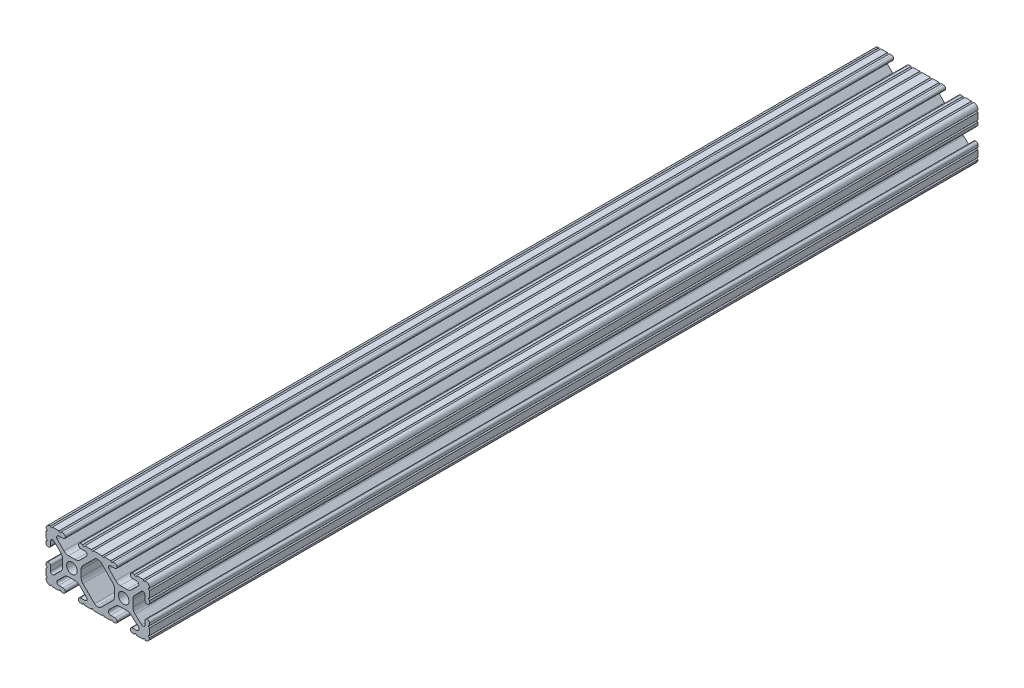
SolidWorks part; units mm, degrees
ref_plane "Front Plane" through (0, 0, 0) normal (0, 0, 1) x (1, 0, 0)
ref_plane "Top Plane" through (0, 0, 0) normal (0, 1, 0) x (1, 0, 0)
ref_plane "Right Plane" through (0, 0, 0) normal (1, 0, 0) x (0, 0, -1)
sketch "Sketch1" plane through (0, 0, 0) normal (0, 0, 1) x (1, 0, 0)
  line L0 (-7.2595, -3.8694) -> (-1.5457, -9.5728)
  line L1 (-8.1915, 1.6223) -> (-8.1915, -1.6223)
  line L2 (-1.504, 9.5765) -> (-7.252, 3.8768)
  line L3 (0.5515, 10.033) -> (-0.3952, 10.033)
  line L4 (7.2829, 3.8459) -> (1.6756, 9.5611)
  line L5 (8.1915, -1.6223) -> (8.1915, 1.6223)
  line L6 (1.5457, -9.5728) -> (7.2595, -3.8694)
  line L7 (-0.4332, -10.033) -> (0.4332, -10.033)
  line L8 (18.0171, 12.7) -> (16.9875, 12.7)
  line L9 (15.9385, 11.651) -> (15.9385, 11.5392)
  line L10 (16.9875, 10.4902) -> (19.1164, 10.4902)
  line L11 (19.8441, 8.7652) -> (16.619, 5.4551)
  line L12 (14.3449, 4.4958) -> (11.0833, 4.4958)
  line L13 (8.817, 5.4472) -> (5.5642, 8.7627)
  line L14 (6.2894, 10.4902) -> (8.4125, 10.4902)
  line L15 (9.4615, 11.5392) -> (9.4615, 11.651)
  line L16 (8.4125, 12.7) -> (7.3829, 12.7)
  line L17 (6.3669, 12.7) -> (3.1496, 12.7)
  line L18 (2.1336, 12.7) -> (-2.1336, 12.7)
  line L19 (-3.1496, 12.7) -> (-6.3669, 12.7)
  line L20 (-7.3829, 12.7) -> (-8.4125, 12.7)
  line L21 (-9.4615, 11.651) -> (-9.4615, 11.5392)
  line L22 (-8.4125, 10.4902) -> (-6.2836, 10.4902)
  line L23 (-5.5326, 8.6661) -> (-8.81, 5.4163)
  line L24 (-11.0455, 4.4958) -> (-14.3545, 4.4958)
  line L25 (-16.59, 5.4163) -> (-19.8674, 8.6661)
  line L26 (-19.1164, 10.4902) -> (-16.9875, 10.4902)
  line L27 (-15.9385, 11.5392) -> (-15.9385, 11.651)
  line L28 (-16.9875, 12.7) -> (-18.0171, 12.7)
  line L29 (-19.0331, 12.7) -> (-22.2504, 12.7)
  line L30 (-25.4, 9.5504) -> (-25.4, 6.3331)
  line L31 (-25.4, 5.3171) -> (-25.4, 4.2375)
  line L32 (-24.401, 3.2385) -> (-24.2392, 3.2385)
  line L33 (-23.1902, 4.2875) -> (-23.1902, 6.3347)
  line L34 (-21.434, 7.0665) -> (-18.148, 3.8082)
  line L35 (-17.2085, 1.5536) -> (-17.2085, -1.6952)
  line L36 (-18.1405, -3.9423) -> (-21.4316, -7.2274)
  line L37 (-23.1902, -6.498) -> (-23.1902, -4.2875)
  line L38 (-24.2392, -3.2385) -> (-24.351, -3.2385)
  line L39 (-25.4, -4.2875) -> (-25.4, -5.3171)
  line L40 (-25.4, -6.3331) -> (-25.4, -9.5504)
  line L41 (-22.2504, -12.7) -> (-19.0331, -12.7)
  line L42 (-18.0171, -12.7) -> (-16.9875, -12.7)
  line L43 (-15.9384, -11.651) -> (-15.9384, -11.5392)
  line L44 (-16.9875, -10.4902) -> (-19.1164, -10.4902)
  line L45 (-19.8341, -8.7551) -> (-16.4966, -5.4237)
  line L46 (-14.2536, -4.4958) -> (-11.1464, -4.4958)
  line L47 (-8.9034, -5.4237) -> (-5.5659, -8.7551)
  line L48 (-6.2836, -10.4902) -> (-8.4125, -10.4902)
  line L49 (-9.4616, -11.5392) -> (-9.4616, -11.651)
  line L50 (-8.4125, -12.7) -> (-7.3829, -12.7)
  line L51 (-6.3669, -12.7) -> (-3.1496, -12.7)
  line L52 (-2.1336, -12.7) -> (2.1336, -12.7)
  line L53 (3.1496, -12.7) -> (6.3669, -12.7)
  line L54 (7.3829, -12.7) -> (8.4125, -12.7)
  line L55 (9.4616, -11.651) -> (9.4616, -11.5392)
  line L56 (8.4125, -10.4902) -> (6.2894, -10.4902)
  line L57 (5.4807, -8.5353) -> (8.5979, -5.4237)
  line L58 (10.8409, -4.4958) -> (14.1026, -4.4958)
  line L59 (16.1879, -5.2766) -> (19.8682, -8.4822)
  line L60 (19.1164, -10.4902) -> (16.9875, -10.4902)
  line L61 (15.9384, -11.5392) -> (15.9384, -11.651)
  line L62 (16.9875, -12.7) -> (18.0171, -12.7)
  line L63 (19.0331, -12.7) -> (22.2504, -12.7)
  line L64 (25.4, -9.5504) -> (25.4, -6.3331)
  line L65 (25.4, -5.3171) -> (25.4, -4.2375)
  line L66 (24.401, -3.2385) -> (24.1892, -3.2385)
  line L67 (23.1902, -4.2375) -> (23.1902, -6.1559)
  line L68 (21.584, -6.8869) -> (18.2982, -4.025)
  line L69 (17.2085, -1.6308) -> (17.2085, 1.6308)
  line L70 (18.1094, 3.8465) -> (21.5263, 7.3534)
  line L71 (23.1902, 6.6769) -> (23.1902, 4.2375)
  line L72 (24.1892, 3.2385) -> (24.401, 3.2385)
  line L73 (25.4, 4.2375) -> (25.4, 5.3171)
  line L74 (25.4, 6.3332) -> (25.4, 9.5504)
  line L75 (22.2504, 12.7) -> (19.0331, 12.7)
  circle A0 centre (-12.7, 0) radius 2.6035
  circle A1 centre (12.7, 0) radius 2.6035
  arc A2 (-1.5457, -9.5728) -> (-0.4332, -10.033) centre (-0.4332, -8.4582) ccw
  arc A3 (-8.1915, -1.6223) -> (-7.2595, -3.8694) centre (-5.0165, -1.6223) ccw
  arc A4 (-7.252, 3.8768) -> (-8.1915, 1.6223) centre (-5.0165, 1.6223) ccw
  arc A5 (-0.3952, 10.033) -> (-1.504, 9.5765) centre (-0.3952, 8.4582) ccw
  arc A6 (1.6756, 9.5611) -> (0.5515, 10.033) centre (0.5515, 8.4582) ccw
  arc A7 (8.1915, 1.6223) -> (7.2829, 3.8459) centre (5.0165, 1.6223) ccw
  arc A8 (7.2595, -3.8694) -> (8.1915, -1.6223) centre (5.0165, -1.6223) ccw
  arc A9 (0.4332, -10.033) -> (1.5457, -9.5728) centre (0.4332, -8.4582) ccw
  arc A10 (18.0171, 12.7) -> (19.0331, 12.7) centre (18.5251, 12.7) ccw
  arc A11 (16.9875, 12.7) -> (15.9385, 11.651) centre (16.9875, 11.651) ccw
  arc A12 (15.9385, 11.5392) -> (16.9875, 10.4902) centre (16.9875, 11.5392) ccw
  arc A13 (19.8441, 8.7652) -> (19.1164, 10.4902) centre (19.1164, 9.4742) ccw
  arc A14 (14.3449, 4.4958) -> (16.619, 5.4551) centre (14.3449, 7.6708) ccw
  arc A15 (8.817, 5.4472) -> (11.0833, 4.4958) centre (11.0833, 7.6708) ccw
  arc A16 (6.2894, 10.4902) -> (5.5642, 8.7627) centre (6.2894, 9.4742) ccw
  arc A17 (8.4125, 10.4902) -> (9.4615, 11.5392) centre (8.4125, 11.5392) ccw
  arc A18 (9.4615, 11.651) -> (8.4125, 12.7) centre (8.4125, 11.651) ccw
  arc A19 (6.3669, 12.7) -> (7.3829, 12.7) centre (6.8749, 12.7) ccw
  arc A20 (2.1336, 12.7) -> (3.1496, 12.7) centre (2.6416, 12.7) ccw
  arc A21 (-3.1496, 12.7) -> (-2.1336, 12.7) centre (-2.6416, 12.7) ccw
  arc A22 (-7.3829, 12.7) -> (-6.3669, 12.7) centre (-6.8749, 12.7) ccw
  arc A23 (-8.4125, 12.7) -> (-9.4615, 11.651) centre (-8.4125, 11.651) ccw
  arc A24 (-9.4615, 11.5392) -> (-8.4125, 10.4902) centre (-8.4125, 11.5392) ccw
  arc A25 (-5.5326, 8.6661) -> (-6.2836, 10.4902) centre (-6.2836, 9.4235) ccw
  arc A26 (-11.0455, 4.4958) -> (-8.81, 5.4163) centre (-11.0455, 7.6708) ccw
  arc A27 (-16.59, 5.4163) -> (-14.3545, 4.4958) centre (-14.3545, 7.6708) ccw
  arc A28 (-19.1164, 10.4902) -> (-19.8674, 8.6661) centre (-19.1164, 9.4235) ccw
  arc A29 (-16.9875, 10.4902) -> (-15.9385, 11.5392) centre (-16.9875, 11.5392) ccw
  arc A30 (-15.9385, 11.651) -> (-16.9875, 12.7) centre (-16.9875, 11.651) ccw
  arc A31 (-19.0331, 12.7) -> (-18.0171, 12.7) centre (-18.5251, 12.7) ccw
  arc A32 (-23.2664, 12.6998) -> (-22.2504, 12.7) centre (-22.7584, 12.7) ccw
  arc A33 (-23.2664, 12.6998) -> (-25.3998, 10.5664) centre (-23.2918, 10.5918) ccw
  arc A34 (-25.4, 9.5504) -> (-25.3998, 10.5664) centre (-25.4, 10.0584) ccw
  arc A35 (-25.4, 5.3171) -> (-25.4, 6.3331) centre (-25.4, 5.8251) ccw
  arc A36 (-25.4, 4.2375) -> (-24.401, 3.2385) centre (-24.401, 4.2375) ccw
  arc A37 (-24.2392, 3.2385) -> (-23.1902, 4.2875) centre (-24.2392, 4.2875) ccw
  arc A38 (-21.434, 7.0665) -> (-23.1902, 6.3347) centre (-22.1596, 6.3347) ccw
  arc A39 (-17.2085, 1.5536) -> (-18.148, 3.8082) centre (-20.3835, 1.5536) ccw
  arc A40 (-18.1405, -3.9423) -> (-17.2085, -1.6952) centre (-20.3835, -1.6952) ccw
  arc A41 (-23.1902, -6.498) -> (-21.4316, -7.2274) centre (-22.1596, -6.498) ccw
  arc A42 (-23.1902, -4.2875) -> (-24.2392, -3.2385) centre (-24.2392, -4.2875) ccw
  arc A43 (-24.351, -3.2385) -> (-25.4, -4.2875) centre (-24.351, -4.2875) ccw
  arc A44 (-25.4, -6.3331) -> (-25.4, -5.3171) centre (-25.4, -5.8251) ccw
  arc A45 (-25.3998, -10.5664) -> (-25.4, -9.5504) centre (-25.4, -10.0584) ccw
  arc A46 (-25.3998, -10.5664) -> (-23.2664, -12.6998) centre (-23.2918, -10.5918) ccw
  arc A47 (-22.2504, -12.7) -> (-23.2664, -12.6998) centre (-22.7584, -12.7) ccw
  arc A48 (-18.0171, -12.7) -> (-19.0331, -12.7) centre (-18.5251, -12.7) ccw
  arc A49 (-16.9875, -12.7) -> (-15.9384, -11.651) centre (-16.9875, -11.651) ccw
  arc A50 (-15.9384, -11.5392) -> (-16.9875, -10.4902) centre (-16.9875, -11.5392) ccw
  arc A51 (-19.8341, -8.7551) -> (-19.1164, -10.4902) centre (-19.1164, -9.4742) ccw
  arc A52 (-14.2536, -4.4958) -> (-16.4966, -5.4237) centre (-14.2536, -7.6708) ccw
  arc A53 (-8.9034, -5.4237) -> (-11.1464, -4.4958) centre (-11.1464, -7.6708) ccw
  arc A54 (-6.2836, -10.4902) -> (-5.5659, -8.7551) centre (-6.2836, -9.4742) ccw
  arc A55 (-8.4125, -10.4902) -> (-9.4616, -11.5392) centre (-8.4125, -11.5392) ccw
  arc A56 (-9.4616, -11.651) -> (-8.4125, -12.7) centre (-8.4125, -11.651) ccw
  arc A57 (-6.3669, -12.7) -> (-7.3829, -12.7) centre (-6.8749, -12.7) ccw
  arc A58 (-2.1336, -12.7) -> (-3.1496, -12.7) centre (-2.6416, -12.7) ccw
  arc A59 (3.1496, -12.7) -> (2.1336, -12.7) centre (2.6416, -12.7) ccw
  arc A60 (7.3829, -12.7) -> (6.3669, -12.7) centre (6.8749, -12.7) ccw
  arc A61 (8.4125, -12.7) -> (9.4616, -11.651) centre (8.4125, -11.651) ccw
  arc A62 (9.4616, -11.5392) -> (8.4125, -10.4902) centre (8.4125, -11.5392) ccw
  arc A63 (5.4807, -8.5353) -> (6.2894, -10.4902) centre (6.2894, -9.3455) ccw
  arc A64 (10.8409, -4.4958) -> (8.5979, -5.4237) centre (10.8409, -7.6708) ccw
  arc A65 (16.1879, -5.2766) -> (14.1026, -4.4958) centre (14.1026, -7.6708) ccw
  arc A66 (19.1164, -10.4902) -> (19.8682, -8.4822) centre (19.1164, -9.3455) ccw
  arc A67 (16.9875, -10.4902) -> (15.9384, -11.5392) centre (16.9875, -11.5392) ccw
  arc A68 (15.9384, -11.651) -> (16.9875, -12.7) centre (16.9875, -11.651) ccw
  arc A69 (19.0331, -12.7) -> (18.0171, -12.7) centre (18.5251, -12.7) ccw
  arc A70 (23.2664, -12.6998) -> (22.2504, -12.7) centre (22.7584, -12.7) ccw
  arc A71 (23.2664, -12.6998) -> (25.3998, -10.5664) centre (23.2918, -10.5918) ccw
  arc A72 (25.4, -9.5504) -> (25.3998, -10.5664) centre (25.4, -10.0584) ccw
  arc A73 (25.4, -5.3171) -> (25.4, -6.3331) centre (25.4, -5.8251) ccw
  arc A74 (25.4, -4.2375) -> (24.401, -3.2385) centre (24.401, -4.2375) ccw
  arc A75 (24.1892, -3.2385) -> (23.1902, -4.2375) centre (24.1892, -4.2375) ccw
  arc A76 (21.584, -6.8869) -> (23.1902, -6.1559) centre (22.2207, -6.1559) ccw
  arc A77 (17.2085, -1.6308) -> (18.2982, -4.025) centre (20.3835, -1.6308) ccw
  arc A78 (18.1094, 3.8465) -> (17.2085, 1.6308) centre (20.3835, 1.6308) ccw
  arc A79 (23.1902, 6.6769) -> (21.5263, 7.3534) centre (22.2207, 6.6769) ccw
  arc A80 (23.1902, 4.2375) -> (24.1892, 3.2385) centre (24.1892, 4.2375) ccw
  arc A81 (24.401, 3.2385) -> (25.4, 4.2375) centre (24.401, 4.2375) ccw
  arc A82 (25.4, 6.3332) -> (25.4, 5.3171) centre (25.4, 5.8251) ccw
  arc A83 (25.3998, 10.5664) -> (25.4, 9.5504) centre (25.4, 10.0584) ccw
  arc A84 (25.3998, 10.5664) -> (23.2664, 12.6998) centre (23.2918, 10.5918) ccw
  arc A85 (22.2504, 12.7) -> (23.2664, 12.6998) centre (22.7584, 12.7) ccw
  point P248 (0, 10.033)
extrude "Boss-Extrude1" add sketch "Sketch1" along normal mid plane 406.4
